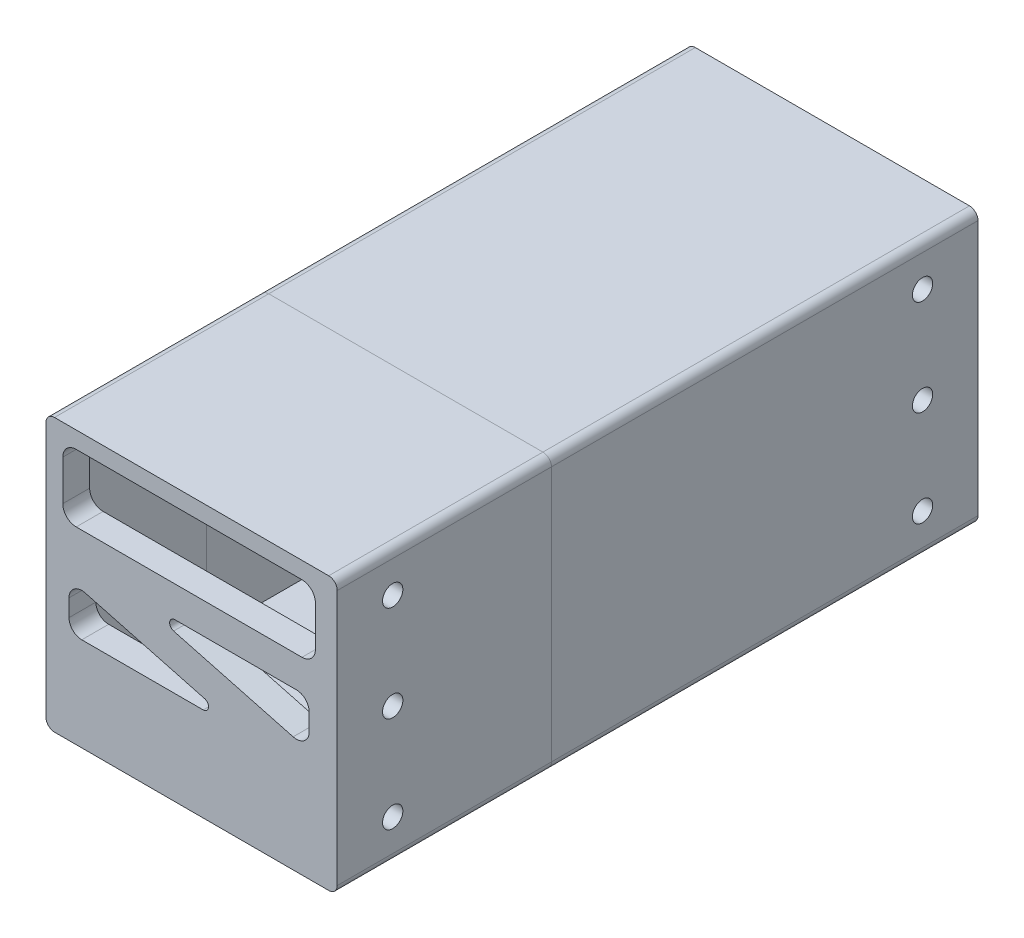
SolidWorks part; units mm, degrees
material "ABS"
ref_plane "X-Y Datum" through (0, 0, 0) normal (0, 0, 1) x (1, 0, 0)
ref_plane "X-Z Datum" through (0, 0, 0) normal (0, 1, 0) x (1, 0, 0)
ref_plane "Y-Z Datum" through (0, 0, 0) normal (1, 0, 0) x (0, 0, -1)
sketch "Sketch1" plane through (0, 0, 0) normal (0, 0, 1) x (1, 0, 0)
  line L0 (-42.608, 40.576) -> (42.608, 40.576)
  line L1 (-38.608, 36.576) -> (38.608, 36.576) construction
  line L2 (-38.608, 36.576) -> (-38.608, -36.576) construction
  line L3 (-38.608, -36.576) -> (38.608, -36.576) construction
  line L4 (38.608, 36.576) -> (38.608, -36.576) construction
  line L5 (-38.608, 36.576) -> (38.608, -36.576) construction
  line L6 (-38.608, -36.576) -> (38.608, 36.576) construction
  line L11 (42.608, 40.576) -> (42.608, -40.576)
  line L12 (-42.608, -40.576) -> (42.608, -40.576)
  line L13 (-42.608, 40.576) -> (-42.608, -40.576)
  point P0 (0, 0)
  point P6 (0, 0)
  dimension "D1" = 77.216
  dimension "D2" = 4
  dimension "D3" = 73.152
extrude "Boss-Extrude1" add sketch "Sketch1" along normal blind 182.776
ref_plane "Plane1" through (0, 0, 127) normal (0, 0, -1) x (-1, 0, 0)
split "Split1" trim tools "Plane1" bodies to split 101 resulting bodies 102 103
shell "Shell2" thickness 4
shell "Shell3" thickness 4
fillet "Fillet1" [suppressed] radius 2.54
fillet "Fillet2" [suppressed] radius 2.54
sketch "Sketch4" plane through (0, 0, 127) normal (0, 0, 1) x (1, 0, 0)
  line L14 (40.608, -38.576) -> (40.608, 38.576)
  line L15 (-40.608, -38.576) -> (40.608, -38.576)
  line L16 (-40.608, 38.576) -> (-40.608, -38.576)
  line L17 (40.608, 38.576) -> (-40.608, 38.576)
  line L18 (40.608, -38.576) -> (40.608, 38.576)
  line L19 (-40.608, -38.576) -> (40.608, -38.576)
  line L20 (-40.608, 38.576) -> (-40.608, -38.576)
  line L21 (40.608, 38.576) -> (-40.608, 38.576)
  line L22 (-38.608, 36.576) -> (-38.608, -36.576)
  line L23 (-38.608, -36.576) -> (38.608, -36.576)
  line L24 (38.608, -36.576) -> (38.608, 36.576)
  line L25 (38.608, 36.576) -> (-38.608, 36.576)
  line L26 (-38.608, 36.576) -> (-38.608, -36.576)
  line L27 (-38.608, -36.576) -> (38.608, -36.576)
  line L28 (38.608, -36.576) -> (38.608, 36.576)
  line L29 (38.608, 36.576) -> (-38.608, 36.576)
  dimension "D1" = 2
  dimension "D2" = 0
extrude "Boss-Extrude2" add sketch "Sketch4" along normal blind 20
sketch "Sketch5" plane through (0, 0, 127) normal (0, 0, -1) x (-1, 0, 0)
  line L0 (40.989, 38.957) -> (-40.989, 38.957)
  line L1 (-40.989, 38.957) -> (-40.989, -38.957)
  line L2 (-40.989, -38.957) -> (40.989, -38.957)
  line L3 (40.989, -38.957) -> (40.989, 38.957)
  line L4 (38.608, -36.576) -> (38.608, 36.576)
  line L5 (-38.608, -36.576) -> (38.608, -36.576)
  line L6 (-38.608, 36.576) -> (-38.608, -36.576)
  line L7 (38.608, 36.576) -> (-38.608, 36.576)
  line L8 (38.608, -36.576) -> (38.608, 36.576)
  line L9 (-38.608, -36.576) -> (38.608, -36.576)
  line L10 (-38.608, 36.576) -> (-38.608, -36.576)
  line L11 (38.608, 36.576) -> (-38.608, 36.576)
  line L12 (-40.608, 38.576) -> (-40.608, -38.576)
  line L13 (-40.608, -38.576) -> (40.608, -38.576)
  line L14 (40.608, -38.576) -> (40.608, 38.576)
  line L15 (40.608, 38.576) -> (-40.608, 38.576)
  line L16 (-40.608, 38.576) -> (-40.608, -38.576) construction
  line L17 (-40.608, -38.576) -> (40.608, -38.576) construction
  line L18 (40.608, -38.576) -> (40.608, 38.576) construction
  line L19 (40.608, 38.576) -> (-40.608, 38.576) construction
  line L24 (-42.608, -40.576) -> (42.608, -40.576)
  line L25 (42.608, -40.576) -> (42.608, 40.576)
  line L26 (42.608, 40.576) -> (-42.608, 40.576)
  line L27 (-42.608, 40.576) -> (-42.608, -40.576)
  line L28 (-42.608, -40.576) -> (42.608, -40.576)
  line L29 (42.608, -40.576) -> (42.608, 40.576)
  line L30 (42.608, 40.576) -> (-42.608, 40.576)
  line L31 (-42.608, 40.576) -> (-42.608, -40.576)
  line M21 (38.608, -36.576) -> (-38.608, -36.576)
  line M22 (-38.608, -36.576) -> (-38.608, 36.576)
  line M23 (-38.608, 36.576) -> (38.608, 36.576)
  line M24 (38.608, 36.576) -> (38.608, -36.576)
  dimension "D1" = 0
  dimension "D2" = 0
  dimension "D3" = 0.381
  dimension "D4" = 0
extrude "Cut-Extrude2" cut sketch "Sketch5" against normal blind 20 contours L2 L3 L0 L1 M24 M21 M22 M23
sketch "Sketch6" plane through (0, 0, 182.776) normal (0, 0, 1) x (1, 0, 0)
  line L0 (0, -40.576) -> (0, 40.576) construction
  line L1 (-42.608, -40.576) -> (42.608, -40.576) construction
  line L2 (42.608, 40.576) -> (-42.608, 40.576) construction
  line L4 (-37.608, 35.576) -> (37.608, 35.576)
  line L5 (-37.608, 35.576) -> (-37.608, 15.576)
  line L6 (-37.608, 15.576) -> (37.608, 15.576)
  line L7 (37.608, 35.576) -> (37.608, 15.576)
  line L8 (-37.608, 35.576) -> (37.608, 15.576) construction
  line L9 (-37.608, 15.576) -> (37.608, 35.576) construction
  line L10 (38.608, 36.576) -> (-38.608, 36.576) construction
  line L11 (38.608, -36.576) -> (38.608, 36.576) construction
  point P6 (0, 25.576)
  dimension "D1" = 20
  dimension "D2" = 1
  dimension "D3" = 1
extrude "Cut-Extrude3" cut sketch "Sketch6" against normal blind 4
fillet "Fillet3" radius 4 4 edges at (37.608, 35.576, 180.776) (37.608, 15.576, 180.776) (-37.608, 35.576, 180.776) (-37.608, 15.576, 180.776)
sketch "Sketch7" plane through (0, 0, 182.776) normal (0, 0, 1) x (1, 0, 0)
  line L0 (-37.608, 31.576) -> (-37.608, 19.576) construction
  line L1 (-33.608, 15.576) -> (33.608, 15.576) construction
  line L2 (33.608, 35.576) -> (-33.608, 35.576) construction
  line L3 (37.608, 19.576) -> (37.608, 31.576) construction
  line L4 (-42.608, 40.576) -> (-42.608, -40.576)
  line L5 (-42.608, -40.576) -> (42.608, -40.576)
  line L6 (42.608, -40.576) -> (42.608, 40.576)
  line L7 (42.608, 40.576) -> (-42.608, 40.576)
  line L8 (-42.608, 40.576) -> (-42.608, -40.576)
  line L9 (-42.608, -40.576) -> (42.608, -40.576)
  line L10 (42.608, -40.576) -> (42.608, 40.576)
  line L11 (42.608, 40.576) -> (-42.608, 40.576)
  line L12 (-33.608, 15.576) -> (33.608, 15.576)
  line L13 (-37.608, 31.576) -> (-37.608, 19.576)
  line L14 (33.608, 35.576) -> (-33.608, 35.576)
  line L15 (37.608, 19.576) -> (37.608, 31.576)
  arc A0 (-37.608, 19.576) -> (-33.608, 15.576) centre (-33.608, 19.576) ccw construction
  arc A1 (-33.608, 35.576) -> (-37.608, 31.576) centre (-33.608, 31.576) ccw construction
  arc A2 (37.608, 31.576) -> (33.608, 35.576) centre (33.608, 31.576) ccw construction
  arc A3 (33.608, 15.576) -> (37.608, 19.576) centre (33.608, 19.576) ccw construction
  arc A12 (-37.608, 19.576) -> (-33.608, 15.576) centre (-33.608, 19.576) ccw
  arc A13 (-33.608, 35.576) -> (-37.608, 31.576) centre (-33.608, 31.576) ccw
  arc A14 (37.608, 31.576) -> (33.608, 35.576) centre (33.608, 31.576) ccw
  arc A15 (33.608, 15.576) -> (37.608, 19.576) centre (33.608, 19.576) ccw
  dimension "D1" = 0
extrude "Boss-Extrude3" add sketch "Sketch7" along normal blind 4
sketch "Sketch8" plane through (0, 0, 0) normal (0, 0, -1) x (-1, 0, 0)
  line L4 (42.608, 40.576) -> (-42.608, 40.576)
  line L5 (-42.608, 40.576) -> (-42.608, -40.576)
  line L6 (-42.608, -40.576) -> (42.608, -40.576)
  line L7 (42.608, -40.576) -> (42.608, 40.576)
  line L8 (42.608, 40.576) -> (-42.608, 40.576)
  line L9 (-42.608, 40.576) -> (-42.608, -40.576)
  line L10 (-42.608, -40.576) -> (42.608, -40.576)
  line L11 (42.608, -40.576) -> (42.608, 40.576)
  dimension "D1" = 0
extrude "Boss-Extrude4" add sketch "Sketch8" along normal blind 4
ref_plane "Plane2" through (0, 0, 91.388) normal (0, 0, 1) x (1, 0, 0)
sketch "Sketch9" plane through (0, 0, 186.776) normal (0, 0, 1) x (1, 0, 0)
  line L0 (-42.608, 0) -> (42.608, 0) construction
  line L1 (-42.608, 40.576) -> (-42.608, -40.576) construction
  line L2 (42.608, -40.576) -> (42.608, 40.576) construction
  line L3 (-42.608, -27.876) -> (42.608, -27.876) construction
  line L4 (-42.608, -40.576) -> (42.608, -40.576) construction
  line L5 (-42.608, -27.876) -> (0, -27.876) construction
  line L6 (0, -27.876) -> (-21.304, -27.876) construction
  line L7 (-21.304, -27.876) -> (-21.304, -24.0766) construction
  line L8 (0, -27.876) -> (42.608, -27.876) construction
  line L9 (21.304, -27.876) -> (21.304, -24.0766) construction
  circle A0 centre (-21.304, -27.876) radius 3.025
  circle A1 centre (0, -27.876) radius 3.025
  circle A2 centre (21.304, -27.876) radius 3.025
  dimension "D2" = 6.05
  dimension "D1" = 12.7
extrude "Cut-Extrude4" cut sketch "Sketch9" against normal blind 6 contours A0 | A1 | A2
mirror "Mirror1" about plane through (0, 0, 91.388) normal (0, 0, 1) of "Cut-Extrude4"
sketch "Sketch10" plane through (0, 0, 4) normal (0, 0, 1) x (1, 0, 0)
  line L4 (-38.608, 36.576) -> (-38.608, -36.576)
  line L5 (-38.608, -36.576) -> (38.608, -36.576)
  line L6 (38.608, -36.576) -> (38.608, 36.576)
  line L7 (38.608, 36.576) -> (-38.608, 36.576)
  line L8 (-38.608, 36.576) -> (-38.608, -36.576)
  line L9 (-38.608, -36.576) -> (38.608, -36.576)
  line L10 (38.608, -36.576) -> (38.608, 36.576)
  line L11 (38.608, 36.576) -> (-38.608, 36.576)
  dimension "D1" = 0
other "Save Bodies1"
extrude "Boss-Extrude5" add sketch "Sketch10" along normal blind 4.5
sketch "Sketch11" plane through (0, 0, -4) normal (0, 0, -1) x (-1, 0, 0)
  line L4 (42.608, 40.576) -> (-42.608, 40.576)
  line L5 (-42.608, 40.576) -> (-42.608, -40.576)
  line L6 (-42.608, -40.576) -> (42.608, -40.576)
  line L7 (42.608, -40.576) -> (42.608, 40.576)
  line L9 (-42.608, 40.576) -> (-42.608, -40.576)
  line L10 (-42.608, -40.576) -> (42.608, -40.576)
  line L11 (42.608, -40.576) -> (42.608, 40.576)
  line L12 (42.608, 40.576) -> (-42.608, 40.576) construction
  line L13 (42.608, 40.576) -> (-42.608, 40.576)
  line L14 (26.098, 27.876) -> (11.7275, 27.876)
  line L15 (-29.908, -1.263) -> (-29.908, -11.766)
  line L16 (29.908, 13.6269) -> (29.908, 24.066)
  line L17 (29.908, -7.7274) -> (29.908, 27.876)
  line L18 (-26.098, -15.576) -> (-11.6396, -15.576)
  line L19 (29.908, 27.876) -> (29.908, -7.7274)
  line L20 (23.8588, 10.5443) -> (9.4882, 20.9835)
  line L21 (-29.908, 27.876) -> (29.908, -15.576)
  line L22 (-29.908, -15.4483) -> (-29.908, 20.0274)
  line L23 (-23.8588, 1.8195) -> (-9.4003, -8.6835)
  line L24 (-29.908, 40.576) -> (-29.908, -40.576) construction
  line L25 (-42.608, -15.576) -> (42.608, -15.576) construction
  line L26 (29.908, -40.576) -> (29.908, 40.576) construction
  line L27 (42.608, 27.876) -> (-42.608, 27.876) construction
  line L28 (-33.6401, 22.7385) -> (26.1759, -20.7135)
  line L29 (-26.1759, 33.0135) -> (33.6401, -10.4385)
  circle A0 centre (21.304, -27.876) radius 3.025 construction
  circle A1 centre (0, -27.876) radius 3.025 construction
  circle A2 centre (-21.304, -27.876) radius 3.025 construction
  circle A3 centre (21.304, -27.876) radius 3.025
  circle A12 centre (0, -27.876) radius 3.025
  circle A13 centre (-21.304, -27.876) radius 3.025
  arc A14 (-29.908, -1.263) -> (-23.8588, 1.8195) centre (-26.098, -1.263) cw
  arc A15 (-26.098, -15.576) -> (-29.908, -11.766) centre (-26.098, -11.766) cw
  arc A16 (-9.4003, -8.6835) -> (-11.6396, -15.576) centre (-11.6396, -11.766) cw
  arc A17 (29.908, 13.6269) -> (23.8588, 10.5443) centre (26.098, 13.6269) cw
  arc A18 (9.4882, 20.9835) -> (11.7275, 27.876) centre (11.7275, 24.066) cw
  arc A19 (26.098, 27.876) -> (29.908, 24.066) centre (26.098, 24.066) cw
  arc A23 (-29.908, 20.0274) -> (-22.4439, 30.3025) centre (-26.1759, 25.1649) cw
  arc A25 (29.908, -7.7274) -> (22.4439, -18.0025) centre (26.1759, -12.8649) cw
  point P38 (-29.908, 20.0274)
  point P60 (29.908, -7.7274)
  dimension "D4" = 17.5777
  dimension "D5" = 17.526
  dimension "D6" = 3.81
  dimension "D1" = 0
  dimension "D2" = 12.7
  dimension "D3" = 25
  dimension "D7" = 6.35
  dimension "D8" = 6.35
extrude "Cut-Extrude5" cut sketch "Sketch11" against normal up to surface (12.5 mm away)
sketch "Sketch12" plane through (0, 0, 186.776) normal (0, 0, 1) x (1, 0, 0)
  line L0 (-30.9726, -0.1002) -> (4.6151, -9.5785)
  line L1 (-4.2066, 6.35) -> (31.9531, 6.35)
  line L2 (-35.7631, -3.7819) -> (-35.7631, -8.89)
  line L3 (-31.9531, -12.7) -> (4.2066, -12.7)
  line L4 (35.7631, 2.54) -> (35.7631, -2.5681)
  line L5 (-35.7631, 6.35) -> (35.7631, -12.7) construction
  line L6 (-35.7631, -12.7) -> (35.7631, 6.35) construction
  line L7 (-4.6151, 3.2285) -> (30.9726, -6.2498)
  line L8 (-34.4763, 11.1816) -> (37.0499, -7.8684) construction
  line L9 (-37.0499, 1.5184) -> (34.4763, -17.5316) construction
  arc A0 (35.7631, -2.5681) -> (30.9726, -6.2498) centre (31.9531, -2.5681) cw
  arc A1 (35.7631, 2.54) -> (31.9531, 6.35) centre (31.9531, 2.54) ccw
  arc A2 (-35.7631, -3.7819) -> (-30.9726, -0.1002) centre (-31.9531, -3.7819) cw
  arc A3 (-31.9531, -12.7) -> (-35.7631, -8.89) centre (-31.9531, -8.89) cw
  arc A4 (4.2066, -12.7) -> (4.6151, -9.5785) centre (4.2066, -11.1125) ccw
  arc A5 (-4.2066, 6.35) -> (-4.6151, 3.2285) centre (-4.2066, 4.7625) ccw
  point P0 (0, -3.175)
  dimension "D2" = 3.81
  dimension "D5" = 1.5875
  dimension "D1" = 3.175
  dimension "D3" = 5
  dimension "D4" = 5
extrude "Cut-Extrude6" cut sketch "Sketch12" against normal up to surface (8 mm away) up to face at (0, 25.576, 178.776)
other "Save Bodies2"
sketch "Sketch13" plane through (42.608, 0, 0) normal (-1, 0, 0) x (0, 0, 1)
  line L1 (127, 40.576) -> (186.776, 40.576)
  line L2 (127, 40.576) -> (127, -40.576)
  line L3 (127, -40.576) -> (186.776, -40.576)
  line L4 (186.776, 40.576) -> (186.776, -40.576)
extrude "Boss-Extrude7" add sketch "Sketch13" against normal blind 1.5
sketch "Sketch15" plane through (42.608, 0, 0) normal (1, 0, 0) x (0, 0, -1)
  line L1 (-127, 40.576) -> (4, 40.576)
  line L2 (-127, 40.576) -> (-127, -40.576)
  line L3 (-127, -40.576) -> (4, -40.576)
  line L4 (4, 40.576) -> (4, -40.576)
extrude "Boss-Extrude8" add sketch "Sketch15" along normal blind 1.5
ref_plane "Plane3" through (0, 0, 123) normal (0, 0, -1) x (-1, 0, 0)
split "Split2" trim tools "Plane3" bodies to split 131 resulting bodies 132 133
sketch "Sketch16" plane through (44.108, 0, 0) normal (1, 0, 0) x (0, 0, -1)
  line L0 (-179.656, 0) -> (49820.344, 0) construction
  line L1 (-186.776, -40.576) -> (-186.776, 40.576) construction
  line L2 (-179.656, 28.575) -> (49820.344, 28.575) construction
  line L3 (-175.6709, -28.575) -> (49824.3291, -28.575) construction
  line L4 (-170.266, 33.6302) -> (-170.266, -49966.3698) construction
  line L5 (-12.51, 35.9206) -> (-12.51, -49964.0794) construction
  line L6 (4, -40.576) -> (4, 40.576) construction
  circle A0 centre (-170.266, 28.575) radius 3.025
  circle A1 centre (-170.266, 0) radius 3.025
  circle A2 centre (-170.266, -28.575) radius 3.025
  circle A3 centre (-12.51, 28.575) radius 3.025
  circle A4 centre (-12.51, 0) radius 3.025
  circle A5 centre (-12.51, -28.575) radius 3.025
  point P4 (-186.776, 0)
  dimension "D1" = 28.575
  dimension "D2" = 28.575
  dimension "D3" = 16.51
  dimension "D4" = 16.51
fillet "Fillet4" radius 2.54 4 edges at (44.108, -40.576, 154.888) (44.108, 40.576, 154.888) (-42.608, 40.576, 154.888) (-42.608, -40.576, 154.888)
fillet "Fillet5" radius 2.54 4 edges at (44.108, 40.576, 59.5) (-42.608, 40.576, 59.5) (44.108, -40.576, 59.5) (-42.608, -40.576, 59.5)
extrude "Cut-Extrude9" cut sketch "Sketch16" against normal blind 19.5
sketch "Sketch18" plane through (0, 0, 186.776) normal (0, 0, 1) x (1, 0, 0)
  line L1 (-30.9166, -18.4897) -> (31.2929, -18.4897)
  line L2 (-30.9166, -18.4897) -> (-30.9166, -35.4334)
  line L3 (-30.9166, -35.4334) -> (31.2929, -35.4334)
  line L4 (31.2929, -18.4897) -> (31.2929, -35.4334)
extrude "Boss-Extrude9" add sketch "Sketch18" against normal blind 8
sketch "Sketch19" plane through (0, 0, -4) normal (0, 0, -1) x (-1, 0, 0)
  line L1 (-31.4166, -20.8396) -> (29.3088, -20.8396)
  line L2 (-31.4166, -20.8396) -> (-31.4166, -35.6808)
  line L3 (-31.4166, -35.6808) -> (29.3088, -35.6808)
  line L4 (29.3088, -20.8396) -> (29.3088, -35.6808)
extrude "Boss-Extrude10" add sketch "Sketch19" against normal blind 12.5
sketch "Sketch20" plane through (0, 0, 123) normal (0, 0, 1) x (1, 0, 0)
  line L11 (-38.608, 36.576) -> (38.608, 36.576)
  line L12 (-38.608, 36.576) -> (-38.608, -36.576)
  line L13 (-38.608, -36.576) -> (38.608, -36.576)
  line L14 (-40.608, -38.576) -> (40.608, -38.576)
  line L15 (40.608, -38.576) -> (40.608, 38.576)
  line L16 (40.608, 38.576) -> (-40.608, 38.576)
  line L17 (-40.608, 38.576) -> (-40.608, -38.576)
  line L18 (-40.608, -38.576) -> (40.608, -38.576)
  line L19 (40.608, -38.576) -> (40.608, 38.576)
  line L20 (40.608, 38.576) -> (-40.608, 38.576)
  line L21 (-40.608, 38.576) -> (-40.608, -38.576)
  line L22 (38.608, 36.576) -> (38.608, -36.576)
  dimension "D1" = 2
extrude "Boss-Extrude11" add sketch "Sketch20" along normal blind 20
sketch "Sketch21" plane through (0, 0, 123) normal (0, 0, -1) x (-1, 0, 0)
  line L18 (-40.608, -38.576) -> (40.608, -38.576)
  line L19 (40.608, -38.576) -> (40.608, 38.576)
  line L20 (40.608, 38.576) -> (-40.608, 38.576)
  line L21 (-40.608, 38.576) -> (-40.608, -38.576)
  line L22 (-40.608, -38.576) -> (40.608, -38.576)
  line L23 (40.608, -38.576) -> (40.608, 38.576)
  line L24 (40.608, 38.576) -> (-40.608, 38.576)
  line L25 (-40.608, 38.576) -> (-40.608, -38.576)
  dimension "D1" = 2
extrude "Cut-Extrude10" cut sketch "Sketch21" against normal blind 20
